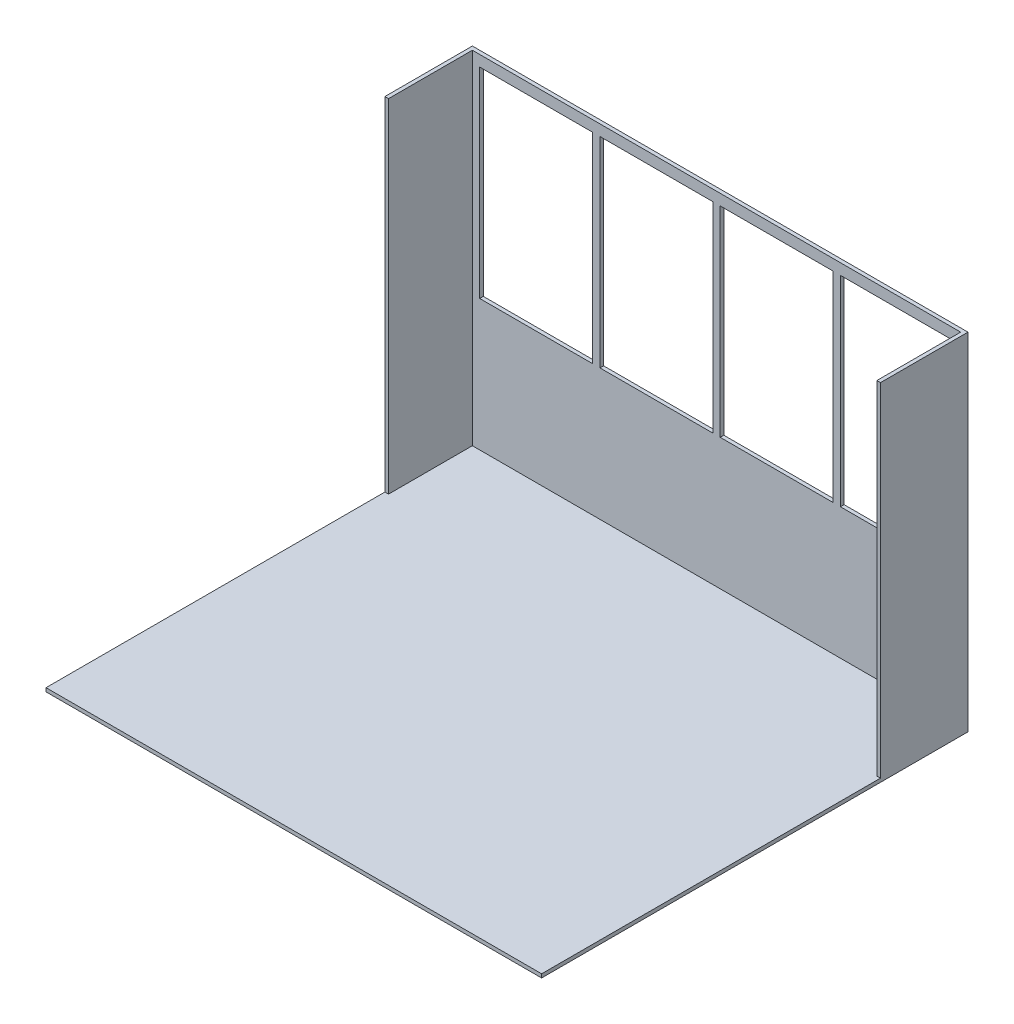
SolidWorks part; units mm, degrees
ref_plane "Front Plane" through (0, 0, 0) normal (0, 0, 1) x (1, 0, 0)
ref_plane "Top Plane" through (0, 0, 0) normal (0, 1, 0) x (1, 0, 0)
ref_plane "Right Plane" through (0, 0, 0) normal (1, 0, 0) x (0, 0, -1)
sketch "Sketch1" plane through (0, 0, 0) normal (0, 1, 0) x (1, 0, 0)
  line L1 (-1727.2, -304.8) -> (1727.2, -304.8)
  line L2 (-1727.2, -304.8) -> (-1727.2, 304.8)
  line L3 (-1727.2, 304.8) -> (1727.2, 304.8)
  line L4 (1727.2, -304.8) -> (1727.2, 304.8)
  line L5 (-1727.2, -304.8) -> (1727.2, 304.8) construction
  line L6 (-1727.2, 304.8) -> (1727.2, -304.8) construction
  point P0 (0, 0)
  dimension "D1" = 3454.4
  dimension "D2" = 609.6
extrude "Boss-Extrude1" add sketch "Sketch1" along normal blind 2413
shell "Shell1" thickness 25.4
sketch "Sketch2" plane through (0, 0, 304.8) normal (0, 0, 1) x (1, 0, 0)
  line L0 (1727.2, 2413) -> (1727.2, 0) construction
  line L1 (-1727.2, 0) -> (1727.2, 0)
  line L2 (-1727.2, 0) -> (-1727.2, 25.4)
  line L3 (-1727.2, 25.4) -> (1727.2, 25.4)
  line L4 (1727.2, 0) -> (1727.2, 25.4)
  line L5 (-1701.8, 25.4) -> (1701.8, 25.4) construction
extrude "Boss-Extrude2" add sketch "Sketch2" along normal blind 2362.2
sketch "Sketch3" plane through (0, 0, -279.4) normal (0, 0, 1) x (1, 0, 0)
  line L0 (-863.6, 2336.8) -> (-1651, 2336.8)
  line L3 (-1651, 939.8) -> (-863.6, 939.8)
  line L4 (-863.6, 2336.8) -> (-863.6, 939.8)
  line L5 (-812.8, 2336.8) -> (-25.4, 2336.8)
  line L6 (-812.8, 2336.8) -> (-812.8, 939.8)
  line L7 (-812.8, 939.8) -> (-25.4, 939.8)
  line L8 (-25.4, 2336.8) -> (-25.4, 939.8)
  line L9 (25.4, 939.8) -> (812.8, 939.8)
  line L10 (25.4, 939.8) -> (25.4, 2336.8)
  line L11 (25.4, 2336.8) -> (812.8, 2336.8)
  line L12 (812.8, 939.8) -> (812.8, 2336.8)
  line L13 (863.6, 2336.8) -> (1651, 2336.8)
  line L14 (863.6, 2336.8) -> (863.6, 939.8)
  line L15 (863.6, 939.8) -> (1651, 939.8)
  line L16 (1651, 2336.8) -> (1651, 939.8)
  line L18 (-1651, 2336.8) -> (-1651, 939.8)
  line L20 (-863.6, 2336.8) -> (-812.8, 2336.8) construction
  line L21 (-25.4, 2336.8) -> (25.4, 2336.8) construction
  line L22 (812.8, 2336.8) -> (863.6, 2336.8) construction
  line L23 (1651, 2336.8) -> (1701.8, 2336.8) construction
  line L24 (1701.8, 2413) -> (1701.8, 25.4) construction
  line L25 (-1701.8, 2336.8) -> (-1651, 2336.8) construction
  line L26 (-1701.8, 2413) -> (-1701.8, 25.4) construction
  line L27 (-1651, 2336.8) -> (-1651, 2387.6) construction
  line L28 (-1701.8, 2387.6) -> (1701.8, 2387.6) construction
  dimension "D1" = 787.4
  dimension "D2" = 1397
extrude "Cut-Extrude1" cut sketch "Sketch3" against normal blind 25.4
ref_plane "Plane1" through (-838.2, 0, 0) normal (1, 0, 0) x (0, 0, -1)
